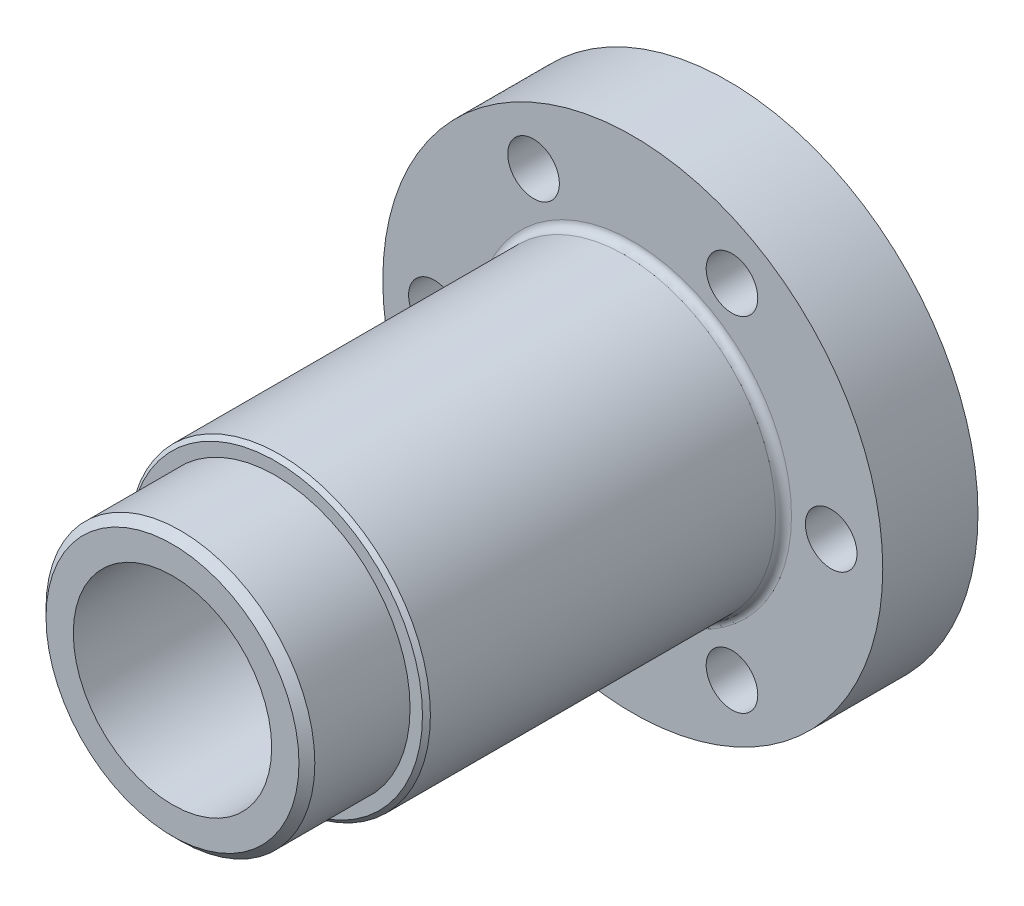
SolidWorks part; units mm, degrees
material "6061-T6 (SS)"
ref_plane "Front Plane" through (0, 0, 0) normal (0, 0, 1) x (1, 0, 0)
ref_plane "Top Plane" through (0, 0, 0) normal (0, 1, 0) x (1, 0, 0)
ref_plane "Right Plane" through (0, 0, 0) normal (1, 0, 0) x (0, 0, -1)
sketch "Sketch1" plane through (0, 0, 0) normal (0, 0, 1) x (1, 0, 0)
  circle A0 centre (0, 0) radius 31.5
  dimension "D1" = 63
extrude "Boss-Extrude1" add sketch "Sketch1" along normal blind 12
sketch "Sketch3" plane through (0, 0, 0) normal (0, 0, -1) x (-1, 0, 0)
  circle A0 centre (0, 0) radius 15.75
  dimension "D1" = 31.5
extrude "Boss-Extrude2" add sketch "Sketch3" along normal blind 6
sketch "Sketch5" plane through (0, 0, 0) normal (0, 0, -1) x (-1, 0, 0)
  line L0 (0, -51.3974) -> (0, 53.1554) construction
  circle A0 centre (0, 25) radius 3
  dimension "D2" = 6
  dimension "D1" = 25
sketch "Sketch9" plane through (0, 0, 12) normal (0, 0, 1) x (1, 0, 0)
  line L1 (-12.5, 21.6506) -> (0, 0) construction
  line L2 (0, -51.3974) -> (0, 53.1554) construction
  circle A0 centre (0, 0) radius 25 construction
  point P3 (-12.5, 21.6506)
  point P7 (12.5, 21.6506)
  point P10 (25, 0)
  point P11 (12.5, -21.6506)
  point P12 (-12.5, -21.6506)
  point P13 (-25, 0)
  point P14 (0, 0)
  dimension "D1" = 30
  dimension "D2" = 50
  dimension "D3" = 6
hole_wizard "Ø6.5 (6.5) Diameter Hole1" positions "Sketch13" profile "Sketch12" hole size "Ø6.5" standard "ANSI Metric" end condition through all
sketch "Sketch13" plane through (0, 0, 12) normal (0, 0, 1) x (1, 0, 0)
  point P0 (-12.5, 21.6506)
  point P3 (-25, 0)
  point P6 (-12.5, -21.6506)
  point P9 (12.5, -21.6506)
  point P12 (25, 0)
  point P15 (12.5, 21.6506)
sketch "Sketch12" plane through (-12.5, 21.6506, 12) normal (1, 0, 0) x (0, -1, 0)
  line L0 (0, 0) -> (0, 18)
  line L1 (0, 18) -> (3.25, 18)
  line L2 (3.25, 18) -> (3.25, 0)
  line L5 (3.25, 0) -> (0, 0)
  line L11 (0, -6.35) -> (0, 107.95) construction
  dimension "Thru Hole Dia." = 6.5
  dimension "Thru Hole Depth" = 18
sketch "Sketch14" plane through (0, 0, 12) normal (0, 0, 1) x (1, 0, 0)
  circle A0 centre (0, 0) radius 19
  dimension "D1" = 38
extrude "Boss-Extrude4" add sketch "Sketch14" along normal blind 45
chamfer "Chamfer2" distance 0.5 angle 45 1 edges at (19, 0, 57)
fillet "Fillet3" radius 1 1 edges at (19, 0, 12)
sketch "Sketch15" plane through (0, 0, 57) normal (0, 0, 1) x (1, 0, 0)
  circle A0 centre (0, 0) radius 16.9375
  dimension "D1" = 33.875
extrude "Boss-Extrude6" add sketch "Sketch15" along normal blind 13
chamfer "Chamfer3" distance 1 angle 45 1 edges at (16.9375, 0, 70)
chamfer "Chamfer6" distance 0.5 angle 45 1 edges at (-15.75, 0, -6)
hole_wizard "Ø25.0mm Dowel Hole1" positions "Sketch17" profile "Sketch16" hole size "Ø25.0" standard "ANSI Metric"
sketch "Sketch17" plane through (0, 0, 70) normal (0, 0, 1) x (1, 0, 0)
  point P0 (0, 0)
sketch "Sketch16" plane through (0, 0, 70) normal (1, 0, 0) x (0, -1, 0)
  line L0 (0, 0) -> (0, 52.5108)
  line L1 (0, 52.5108) -> (12.5, 45)
  line L2 (12.5, 45) -> (12.5, 0)
  line L5 (12.5, 0) -> (0, 0)
  line L10 (0, 52.5108) -> (-12.5, 45) construction
  line L11 (0, -6.35) -> (0, 107.95) construction
  dimension "Hole Dia." = 25
  dimension "Hole Depth" = 45
  dimension "Drill Angle" = 118
